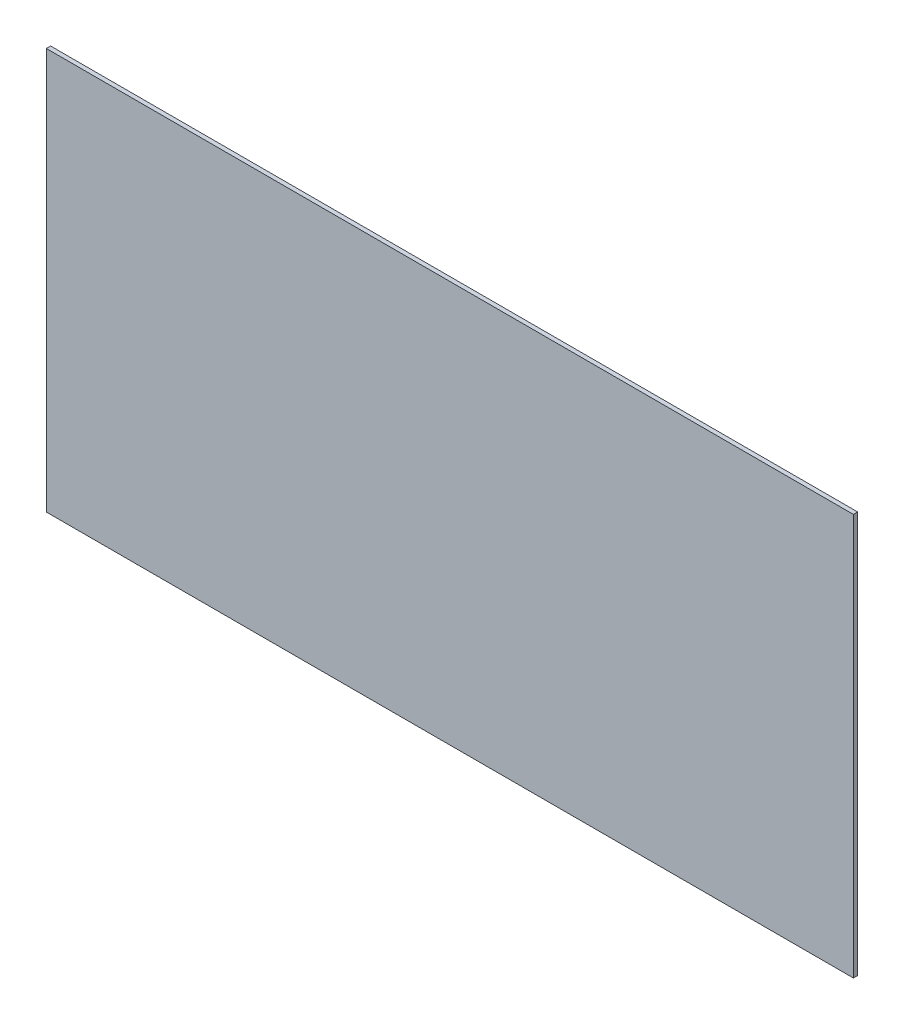
SolidWorks part; units mm, degrees
ref_plane "Plan de face" through (0, 0, 0) normal (0, 0, 1) x (1, 0, 0)
ref_plane "Plan de dessus" through (0, 0, 0) normal (0, 1, 0) x (1, 0, 0)
ref_plane "Plan de droite" through (0, 0, 0) normal (1, 0, 0) x (0, 0, -1)
sketch "Esquisse1" plane through (0, 0, 0) normal (0, 0, 1) x (1, 0, 0)
  line L1 (-132.4099, 76.3067) -> (167.5901, 76.3067)
  line L2 (-132.4099, 76.3067) -> (-132.4099, -72.9433)
  line L3 (-132.4099, -72.9433) -> (167.5901, -72.9433)
  line L4 (167.5901, 76.3067) -> (167.5901, -72.9433)
  dimension "D1" = 149.25
  dimension "D2" = 300
extrude "Boss.-Extru.1" add sketch "Esquisse1" along normal blind 1.5875
